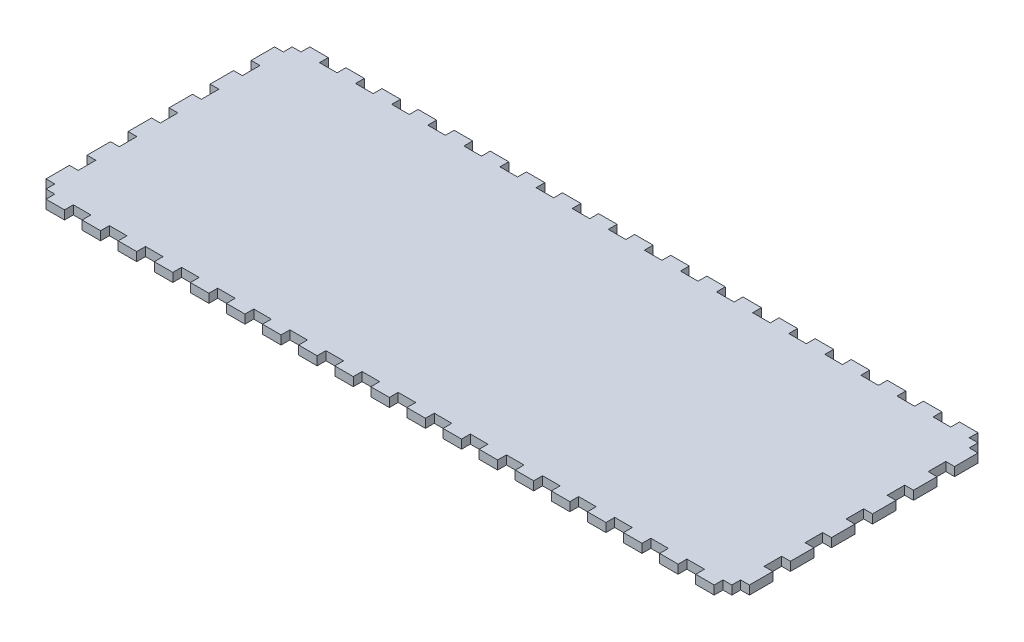
SolidWorks part; units mm, degrees
material "Acrylic (Medium-high impact)"
ref_plane "Front Plane" through (0, 0, 0) normal (0, 0, 1) x (1, 0, 0)
ref_plane "Top Plane" through (0, 0, 0) normal (0, 1, 0) x (1, 0, 0)
ref_plane "Right Plane" through (0, 0, 0) normal (1, 0, 0) x (0, 0, -1)
sketch "Sketch1" plane through (0, 0, 0) normal (0, 1, 0) x (1, 0, 0)
  line L1 (-254, 95.25) -> (254, 95.25)
  line L2 (-254, 95.25) -> (-254, -95.25)
  line L3 (-254, -95.25) -> (254, -95.25)
  line L4 (254, 95.25) -> (254, -95.25)
  point P4 (-254, 0)
  point P6 (0, 95.25)
  dimension "D1" = 190.5
  dimension "D2" = 508
extrude "Boss-Extrude1" add sketch "Sketch1" along normal blind 6.35
sketch "Sketch2" plane through (0, 6.35, 0) normal (0, 1, 0) x (1, 0, 0)
  line L0 (254, -95.25) -> (254, 95.25) construction
  line L1 (-254, 95.25) -> (254, 95.25)
  line L2 (-254, 95.25) -> (-254, -95.25)
  line L3 (-254, -95.25) -> (254, -95.25)
  line L4 (254, 95.25) -> (254, -95.25)
  line L5 (-254, -95.25) -> (254, -95.25) construction
  line L7 (-247.65, 88.9) -> (247.65, 88.9)
  line L8 (-247.65, 88.9) -> (-247.65, -88.9)
  line L9 (-247.65, -88.9) -> (247.65, -88.9)
  line L10 (247.65, 88.9) -> (247.65, -88.9)
  point P7 (-247.65, 0)
  point P14 (-254, 0)
  point P15 (0, -88.9)
  point P16 (0, -95.25)
  point P17 (247.65, 0)
  point P18 (254, 0)
  dimension "D1" = 6.35
  dimension "D2" = 6.35
extrude "Boss-Extrude2" add sketch "Sketch2" along normal blind 298.45
sketch "Sketch3" plane through (0, 0, 95.25) normal (0, 0, 1) x (1, 0, 0)
  line L0 (0, 304.8) -> (0, 0) construction
  line L1 (-254, 304.8) -> (254, 304.8) construction
  line L2 (-247.65, 6.35) -> (247.65, 6.35) construction
  line L4 (-3.302, 283.21) -> (-3.302, 6.35)
  line L5 (-3.302, 6.35) -> (3.302, 6.35)
  line L6 (3.302, 292.354) -> (3.302, 6.35)
  line L7 (3.302, 292.354) -> (-16.256, 292.354)
  line L9 (-5.842, 285.75) -> (-16.256, 285.75)
  line L10 (-16.256, 292.354) -> (-16.256, 285.75)
  line L11 (3.302, 101.6) -> (16.002, 101.6) construction
  line L12 (-254, 0) -> (254, 0) construction
  line L13 (12.827, 88.9) -> (12.827, 101.6) construction
  line L14 (9.652, 88.9) -> (16.002, 88.9)
  line L15 (9.652, 88.9) -> (9.652, 71.9667)
  line L16 (9.652, 71.9667) -> (16.002, 71.9667)
  line L17 (16.002, 88.9) -> (16.002, 71.9667)
  line L18 (9.652, 42.3333) -> (16.002, 42.3333)
  line L19 (9.652, 42.3333) -> (9.652, 59.2667)
  line L20 (9.652, 59.2667) -> (16.002, 59.2667)
  line L21 (16.002, 42.3333) -> (16.002, 59.2667)
  line L26 (9.652, 29.6333) -> (16.002, 29.6333)
  line L27 (9.652, 29.6333) -> (9.652, 12.7)
  line L28 (9.652, 12.7) -> (16.002, 12.7)
  line L29 (16.002, 29.6333) -> (16.002, 12.7)
  line L30 (12.827, 59.2667) -> (12.827, 71.9667) construction
  line L31 (12.827, 29.6333) -> (12.827, 42.3333) construction
  line L32 (12.827, 12.7) -> (12.827, 0) construction
  arc A0 (-3.302, 283.21) -> (-5.842, 285.75) centre (-5.842, 283.21) ccw
  point P5 (0, 6.35)
  dimension "D5" = 2.54
  dimension "D1" = 6.604
  dimension "D2" = 12.954
  dimension "D3" = 6.604
  dimension "D4" = 286.004
  dimension "D6" = 101.6
  dimension "D7" = 12.7
  dimension "D8" = 12.7
  dimension "D9" = 6.35
extrude "Cut-Extrude1" cut sketch "Sketch3" against normal blind 12.7
sketch "Sketch4" plane through (0, 0, -88.9) normal (0, 0, 1) x (1, 0, 0)
  line L0 (-254, 304.8) -> (254, 304.8) construction
  line L1 (-22.606, 304.8) -> (-16.256, 304.8)
  line L2 (-22.606, 304.8) -> (-22.606, 6.35)
  line L3 (-22.606, 6.35) -> (-16.256, 6.35)
  line L4 (-16.256, 304.8) -> (-16.256, 6.35)
  line L5 (6.477, 263.525) -> (6.477, 247.65) construction
  line L6 (-16.256, 292.354) -> (-16.256, 285.75) construction
  line L7 (3.302, 304.8) -> (9.652, 304.8)
  line L8 (3.302, 304.8) -> (3.302, 6.35)
  line L9 (3.302, 6.35) -> (9.652, 6.35)
  line L10 (9.652, 304.8) -> (9.652, 6.35)
  line L11 (247.65, 6.35) -> (-247.65, 6.35) construction
  line L12 (3.302, 6.35) -> (3.302, 292.354) construction
  line L13 (-16.256, 304.8) -> (-22.606, 304.8)
  line L14 (-16.256, 304.8) -> (-16.256, 292.1)
  line L15 (-16.256, 292.1) -> (-22.606, 292.1)
  line L16 (-22.606, 304.8) -> (-22.606, 292.1)
  line L17 (-16.256, 276.225) -> (-22.606, 276.225)
  line L18 (-16.256, 276.225) -> (-16.256, 263.525)
  line L19 (-16.256, 263.525) -> (-22.606, 263.525)
  line L20 (-22.606, 276.225) -> (-22.606, 263.525)
  line L21 (-22.606, 6.35) -> (-16.256, 6.35)
  line L22 (-22.606, 6.35) -> (-22.606, 19.05)
  line L23 (-22.606, 19.05) -> (-16.256, 19.05)
  line L24 (-16.256, 6.35) -> (-16.256, 19.05)
  line L25 (-22.606, 34.925) -> (-16.256, 34.925)
  line L26 (-22.606, 34.925) -> (-22.606, 47.625)
  line L27 (-22.606, 47.625) -> (-16.256, 47.625)
  line L28 (-16.256, 34.925) -> (-16.256, 47.625)
  line L29 (-22.606, 92.075) -> (-16.256, 92.075)
  line L30 (-22.606, 92.075) -> (-22.606, 104.775)
  line L31 (-22.606, 104.775) -> (-16.256, 104.775)
  line L32 (-16.256, 92.075) -> (-16.256, 104.775)
  line L33 (-22.606, 149.225) -> (-16.256, 149.225)
  line L34 (-22.606, 149.225) -> (-22.606, 161.925)
  line L35 (-22.606, 161.925) -> (-16.256, 161.925)
  line L36 (-16.256, 149.225) -> (-16.256, 161.925)
  line L37 (-22.606, 177.8) -> (-16.256, 177.8)
  line L38 (-22.606, 177.8) -> (-22.606, 190.5)
  line L39 (-22.606, 190.5) -> (-16.256, 190.5)
  line L40 (-16.256, 177.8) -> (-16.256, 190.5)
  line L41 (-22.606, 206.375) -> (-16.256, 206.375)
  line L42 (-22.606, 206.375) -> (-22.606, 219.075)
  line L43 (-22.606, 219.075) -> (-16.256, 219.075)
  line L44 (-16.256, 206.375) -> (-16.256, 219.075)
  line L45 (-22.606, 234.95) -> (-16.256, 234.95)
  line L46 (-22.606, 234.95) -> (-22.606, 247.65)
  line L47 (-22.606, 247.65) -> (-16.256, 247.65)
  line L48 (-16.256, 234.95) -> (-16.256, 247.65)
  line L49 (-16.256, 133.35) -> (-22.606, 133.35)
  line L50 (-16.256, 133.35) -> (-16.256, 120.65)
  line L51 (-16.256, 120.65) -> (-22.606, 120.65)
  line L52 (-22.606, 133.35) -> (-22.606, 120.65)
  line L53 (-16.256, 76.2) -> (-22.606, 76.2)
  line L54 (-16.256, 76.2) -> (-16.256, 63.5)
  line L55 (-16.256, 63.5) -> (-22.606, 63.5)
  line L56 (-22.606, 76.2) -> (-22.606, 63.5)
  line L57 (-19.431, 304.8) -> (-19.431, 292.1) construction
  line L58 (-19.431, 292.1) -> (-19.431, 276.225) construction
  line L59 (-19.431, 276.225) -> (-19.431, 263.525) construction
  line L60 (-19.431, 247.65) -> (-19.431, 234.95) construction
  line L61 (-19.431, 234.95) -> (-19.431, 219.075) construction
  line L62 (-19.431, 219.075) -> (-19.431, 206.375) construction
  line L63 (-19.431, 206.375) -> (-19.431, 190.5) construction
  line L64 (-19.431, 190.5) -> (-19.431, 177.8) construction
  line L65 (-19.431, 177.8) -> (-19.431, 161.925) construction
  line L66 (-19.431, 161.925) -> (-19.431, 149.225) construction
  line L67 (-19.431, 133.35) -> (-19.431, 120.65) construction
  line L68 (-19.431, 120.65) -> (-19.431, 104.775) construction
  line L69 (-19.431, 104.775) -> (-19.431, 92.075) construction
  line L70 (-19.431, 92.075) -> (-19.431, 76.2) construction
  line L71 (-19.431, 76.2) -> (-19.431, 63.5) construction
  line L72 (-19.431, 63.5) -> (-19.431, 47.625) construction
  line L73 (-19.431, 47.625) -> (-19.431, 34.925) construction
  line L74 (-19.431, 34.925) -> (-19.431, 19.05) construction
  line L75 (-19.431, 19.05) -> (-19.431, 6.35) construction
  line L76 (-19.431, 149.225) -> (-19.431, 133.35) construction
  line L77 (-19.431, 263.525) -> (-19.431, 247.65) construction
  line L78 (-6.477, 304.8) -> (-6.477, 0) construction
  line L79 (254, 304.8) -> (-254, 304.8) construction
  line L80 (254, 0) -> (-254, 0) construction
  line L81 (-6.477, 8.3493) -> (3.302, 8.3493) construction
  line L82 (-6.477, 8.3493) -> (-16.256, 8.3493) construction
  line L83 (6.477, 149.225) -> (6.477, 133.35) construction
  line L84 (6.477, 19.05) -> (6.477, 6.35) construction
  line L85 (6.477, 34.925) -> (6.477, 19.05) construction
  line L86 (6.477, 47.625) -> (6.477, 34.925) construction
  line L87 (6.477, 63.5) -> (6.477, 47.625) construction
  line L88 (6.477, 76.2) -> (6.477, 63.5) construction
  line L89 (6.477, 92.075) -> (6.477, 76.2) construction
  line L90 (6.477, 104.775) -> (6.477, 92.075) construction
  line L91 (6.477, 120.65) -> (6.477, 104.775) construction
  line L92 (6.477, 133.35) -> (6.477, 120.65) construction
  line L93 (6.477, 161.925) -> (6.477, 149.225) construction
  line L94 (6.477, 177.8) -> (6.477, 161.925) construction
  line L95 (6.477, 190.5) -> (6.477, 177.8) construction
  line L96 (6.477, 206.375) -> (6.477, 190.5) construction
  line L97 (6.477, 219.075) -> (6.477, 206.375) construction
  line L98 (6.477, 234.95) -> (6.477, 219.075) construction
  line L99 (6.477, 247.65) -> (6.477, 234.95) construction
  line L100 (6.477, 276.225) -> (6.477, 263.525) construction
  line L101 (6.477, 292.1) -> (6.477, 276.225) construction
  line L102 (6.477, 304.8) -> (6.477, 292.1) construction
  line L103 (9.652, 76.2) -> (9.652, 63.5)
  line L104 (3.302, 63.5) -> (9.652, 63.5)
  line L105 (3.302, 76.2) -> (3.302, 63.5)
  line L106 (3.302, 76.2) -> (9.652, 76.2)
  line L107 (9.652, 133.35) -> (9.652, 120.65)
  line L108 (3.302, 120.65) -> (9.652, 120.65)
  line L109 (3.302, 133.35) -> (3.302, 120.65)
  line L110 (3.302, 133.35) -> (9.652, 133.35)
  line L111 (3.302, 234.95) -> (3.302, 247.65)
  line L112 (9.652, 247.65) -> (3.302, 247.65)
  line L113 (9.652, 234.95) -> (9.652, 247.65)
  line L114 (9.652, 234.95) -> (3.302, 234.95)
  line L115 (3.302, 206.375) -> (3.302, 219.075)
  line L116 (9.652, 219.075) -> (3.302, 219.075)
  line L117 (9.652, 206.375) -> (9.652, 219.075)
  line L118 (9.652, 206.375) -> (3.302, 206.375)
  line L119 (3.302, 177.8) -> (3.302, 190.5)
  line L120 (9.652, 190.5) -> (3.302, 190.5)
  line L121 (9.652, 177.8) -> (9.652, 190.5)
  line L122 (9.652, 177.8) -> (3.302, 177.8)
  line L123 (3.302, 149.225) -> (3.302, 161.925)
  line L124 (9.652, 161.925) -> (3.302, 161.925)
  line L125 (9.652, 149.225) -> (9.652, 161.925)
  line L126 (9.652, 149.225) -> (3.302, 149.225)
  line L127 (3.302, 92.075) -> (3.302, 104.775)
  line L128 (9.652, 104.775) -> (3.302, 104.775)
  line L129 (9.652, 92.075) -> (9.652, 104.775)
  line L130 (9.652, 92.075) -> (3.302, 92.075)
  line L131 (3.302, 34.925) -> (3.302, 47.625)
  line L132 (9.652, 47.625) -> (3.302, 47.625)
  line L133 (9.652, 34.925) -> (9.652, 47.625)
  line L134 (9.652, 34.925) -> (3.302, 34.925)
  line L135 (3.302, 6.35) -> (3.302, 19.05)
  line L136 (9.652, 19.05) -> (3.302, 19.05)
  line L137 (9.652, 6.35) -> (9.652, 19.05)
  line L138 (9.652, 6.35) -> (3.302, 6.35)
  line L139 (9.652, 276.225) -> (9.652, 263.525)
  line L140 (3.302, 263.525) -> (9.652, 263.525)
  line L141 (3.302, 276.225) -> (3.302, 263.525)
  line L142 (3.302, 276.225) -> (9.652, 276.225)
  line L143 (9.652, 304.8) -> (9.652, 292.1)
  line L144 (3.302, 292.1) -> (9.652, 292.1)
  line L145 (3.302, 304.8) -> (3.302, 292.1)
  line L146 (3.302, 304.8) -> (9.652, 304.8)
  line L147 (3.302, 304.8) -> (3.302, 6.35)
  line L148 (9.652, 6.35) -> (3.302, 6.35)
  line L149 (9.652, 304.8) -> (9.652, 6.35)
  line L150 (9.652, 304.8) -> (3.302, 304.8)
  point P14 (-16.256, 289.052)
  dimension "D1" = 6.35
  dimension "D2" = 12.7
extrude "Cut-Extrude2" cut sketch "Sketch4" against normal up to next (6.35 mm away) contours L17 L4 L15 L2 | L2 L47 L4 L19 | L45 L2 L43 L4 | L41 L2 L39 L4 | L37 L2 L35 L4 | L49 L4 L33 L2 | L4 L51 L2 L31 | L53 L4 L29 L2 | L4 L55 L2 L27 | L25 L2 L23 L4
ref_plane "Plane1" through (-6.477, 0, 0) normal (-1, 0, 0) x (0, 0, 1)
mirror "Mirror1" about plane through (-6.477, 0, 0) normal (-1, 0, 0) of "Cut-Extrude2"
sketch "Sketch5" plane through (0, 0, 0) normal (0, -1, 0) x (-1, 0, 0)
  line L0 (-227.9316, -95.25) -> (-227.9316, -88.9)
  line L1 (-247.65, 88.9) -> (247.65, 88.9)
  line L2 (-247.65, 88.9) -> (-247.65, -88.9)
  line L3 (-247.65, -88.9) -> (247.65, -88.9)
  line L4 (247.65, 88.9) -> (247.65, -88.9)
  line L5 (-254, -95.25) -> (-241.3, -95.25)
  line L6 (-254, -95.25) -> (-254, -88.9)
  line L7 (-254, -88.9) -> (-241.3, -88.9)
  line L8 (-241.3, -95.25) -> (-241.3, -88.9)
  line L9 (-227.9316, -95.25) -> (-215.2316, -95.25)
  line L10 (-227.9316, -88.9) -> (-215.2316, -88.9)
  line L11 (-215.2316, -95.25) -> (-215.2316, -88.9)
  line L12 (-201.8632, -95.25) -> (-201.8632, -88.9)
  line L13 (-201.8632, -95.25) -> (-189.1632, -95.25)
  line L14 (-201.8632, -88.9) -> (-189.1632, -88.9)
  line L15 (-189.1632, -95.25) -> (-189.1632, -88.9)
  line L16 (-175.7947, -95.25) -> (-175.7947, -88.9)
  line L17 (-175.7947, -95.25) -> (-163.0947, -95.25)
  line L18 (-175.7947, -88.9) -> (-163.0947, -88.9)
  line L19 (-163.0947, -95.25) -> (-163.0947, -88.9)
  line L20 (-149.7263, -95.25) -> (-149.7263, -88.9)
  line L21 (-149.7263, -95.25) -> (-137.0263, -95.25)
  line L22 (-149.7263, -88.9) -> (-137.0263, -88.9)
  line L23 (-137.0263, -95.25) -> (-137.0263, -88.9)
  line L24 (-123.6579, -95.25) -> (-123.6579, -88.9)
  line L25 (-123.6579, -95.25) -> (-110.9579, -95.25)
  line L26 (-123.6579, -88.9) -> (-110.9579, -88.9)
  line L27 (-110.9579, -95.25) -> (-110.9579, -88.9)
  line L28 (-97.5895, -95.25) -> (-97.5895, -88.9)
  line L29 (-97.5895, -95.25) -> (-84.8895, -95.25)
  line L30 (-97.5895, -88.9) -> (-84.8895, -88.9)
  line L31 (-84.8895, -95.25) -> (-84.8895, -88.9)
  line L32 (-71.5211, -95.25) -> (-71.5211, -88.9)
  line L33 (-71.5211, -95.25) -> (-58.8211, -95.25)
  line L34 (-71.5211, -88.9) -> (-58.8211, -88.9)
  line L35 (-58.8211, -95.25) -> (-58.8211, -88.9)
  line L36 (-45.4526, -95.25) -> (-45.4526, -88.9)
  line L37 (-45.4526, -95.25) -> (-32.7526, -95.25)
  line L38 (-45.4526, -88.9) -> (-32.7526, -88.9)
  line L39 (-32.7526, -95.25) -> (-32.7526, -88.9)
  line L40 (-19.3842, -95.25) -> (-19.3842, -88.9)
  line L41 (-19.3842, -95.25) -> (-6.6842, -95.25)
  line L42 (-19.3842, -88.9) -> (-6.6842, -88.9)
  line L43 (-6.6842, -95.25) -> (-6.6842, -88.9)
  line L44 (6.6842, -95.25) -> (6.6842, -88.9)
  line L45 (6.6842, -95.25) -> (19.3842, -95.25)
  line L46 (6.6842, -88.9) -> (19.3842, -88.9)
  line L47 (19.3842, -95.25) -> (19.3842, -88.9)
  line L48 (32.7526, -95.25) -> (32.7526, -88.9)
  line L49 (32.7526, -95.25) -> (45.4526, -95.25)
  line L50 (32.7526, -88.9) -> (45.4526, -88.9)
  line L51 (45.4526, -95.25) -> (45.4526, -88.9)
  line L52 (58.8211, -95.25) -> (58.8211, -88.9)
  line L53 (58.8211, -95.25) -> (71.5211, -95.25)
  line L54 (58.8211, -88.9) -> (71.5211, -88.9)
  line L55 (71.5211, -95.25) -> (71.5211, -88.9)
  line L56 (84.8895, -95.25) -> (84.8895, -88.9)
  line L57 (84.8895, -95.25) -> (97.5895, -95.25)
  line L58 (84.8895, -88.9) -> (97.5895, -88.9)
  line L59 (97.5895, -95.25) -> (97.5895, -88.9)
  line L60 (110.9579, -95.25) -> (110.9579, -88.9)
  line L61 (110.9579, -95.25) -> (123.6579, -95.25)
  line L62 (110.9579, -88.9) -> (123.6579, -88.9)
  line L63 (123.6579, -95.25) -> (123.6579, -88.9)
  line L64 (137.0263, -95.25) -> (137.0263, -88.9)
  line L65 (137.0263, -95.25) -> (149.7263, -95.25)
  line L66 (137.0263, -88.9) -> (149.7263, -88.9)
  line L67 (149.7263, -95.25) -> (149.7263, -88.9)
  line L68 (163.0947, -95.25) -> (163.0947, -88.9)
  line L69 (163.0947, -95.25) -> (175.7947, -95.25)
  line L70 (163.0947, -88.9) -> (175.7947, -88.9)
  line L71 (175.7947, -95.25) -> (175.7947, -88.9)
  line L72 (189.1632, -95.25) -> (189.1632, -88.9)
  line L73 (189.1632, -95.25) -> (201.8632, -95.25)
  line L74 (189.1632, -88.9) -> (201.8632, -88.9)
  line L75 (201.8632, -95.25) -> (201.8632, -88.9)
  line L76 (215.2316, -95.25) -> (215.2316, -88.9)
  line L77 (215.2316, -95.25) -> (227.9316, -95.25)
  line L78 (215.2316, -88.9) -> (227.9316, -88.9)
  line L79 (227.9316, -95.25) -> (227.9316, -88.9)
  line L80 (241.3, -95.25) -> (241.3, -88.9)
  line L81 (241.3, -95.25) -> (254, -95.25)
  line L82 (241.3, -88.9) -> (254, -88.9)
  line L83 (254, -95.25) -> (254, -88.9)
  line L84 (-167.64, 0) -> (167.64, 0) construction
  line L85 (254, 95.25) -> (254, 88.9)
  line L86 (241.3, 88.9) -> (254, 88.9)
  line L87 (241.3, 95.25) -> (254, 95.25)
  line L88 (241.3, 95.25) -> (241.3, 88.9)
  line L89 (227.9316, 95.25) -> (227.9316, 88.9)
  line L90 (215.2316, 88.9) -> (227.9316, 88.9)
  line L91 (215.2316, 95.25) -> (227.9316, 95.25)
  line L92 (215.2316, 95.25) -> (215.2316, 88.9)
  line L93 (201.8632, 95.25) -> (201.8632, 88.9)
  line L94 (189.1632, 88.9) -> (201.8632, 88.9)
  line L95 (189.1632, 95.25) -> (201.8632, 95.25)
  line L96 (189.1632, 95.25) -> (189.1632, 88.9)
  line L97 (175.7947, 95.25) -> (175.7947, 88.9)
  line L98 (163.0947, 88.9) -> (175.7947, 88.9)
  line L99 (163.0947, 95.25) -> (175.7947, 95.25)
  line L100 (163.0947, 95.25) -> (163.0947, 88.9)
  line L101 (149.7263, 95.25) -> (149.7263, 88.9)
  line L102 (137.0263, 88.9) -> (149.7263, 88.9)
  line L103 (137.0263, 95.25) -> (149.7263, 95.25)
  line L104 (137.0263, 95.25) -> (137.0263, 88.9)
  line L105 (123.6579, 95.25) -> (123.6579, 88.9)
  line L106 (110.9579, 88.9) -> (123.6579, 88.9)
  line L107 (110.9579, 95.25) -> (123.6579, 95.25)
  line L108 (110.9579, 95.25) -> (110.9579, 88.9)
  line L109 (97.5895, 95.25) -> (97.5895, 88.9)
  line L110 (84.8895, 88.9) -> (97.5895, 88.9)
  line L111 (84.8895, 95.25) -> (97.5895, 95.25)
  line L112 (84.8895, 95.25) -> (84.8895, 88.9)
  line L113 (71.5211, 95.25) -> (71.5211, 88.9)
  line L114 (58.8211, 88.9) -> (71.5211, 88.9)
  line L115 (58.8211, 95.25) -> (71.5211, 95.25)
  line L116 (58.8211, 95.25) -> (58.8211, 88.9)
  line L117 (45.4526, 95.25) -> (45.4526, 88.9)
  line L118 (32.7526, 88.9) -> (45.4526, 88.9)
  line L119 (32.7526, 95.25) -> (45.4526, 95.25)
  line L120 (32.7526, 95.25) -> (32.7526, 88.9)
  line L121 (19.3842, 95.25) -> (19.3842, 88.9)
  line L122 (6.6842, 88.9) -> (19.3842, 88.9)
  line L123 (6.6842, 95.25) -> (19.3842, 95.25)
  line L124 (6.6842, 95.25) -> (6.6842, 88.9)
  line L125 (-6.6842, 95.25) -> (-6.6842, 88.9)
  line L126 (-19.3842, 88.9) -> (-6.6842, 88.9)
  line L127 (-19.3842, 95.25) -> (-6.6842, 95.25)
  line L128 (-19.3842, 95.25) -> (-19.3842, 88.9)
  line L129 (-32.7526, 95.25) -> (-32.7526, 88.9)
  line L130 (-45.4526, 88.9) -> (-32.7526, 88.9)
  line L131 (-45.4526, 95.25) -> (-32.7526, 95.25)
  line L132 (-45.4526, 95.25) -> (-45.4526, 88.9)
  line L133 (-58.8211, 95.25) -> (-58.8211, 88.9)
  line L134 (-71.5211, 88.9) -> (-58.8211, 88.9)
  line L135 (-71.5211, 95.25) -> (-58.8211, 95.25)
  line L136 (-71.5211, 95.25) -> (-71.5211, 88.9)
  line L137 (-84.8895, 95.25) -> (-84.8895, 88.9)
  line L138 (-97.5895, 88.9) -> (-84.8895, 88.9)
  line L139 (-97.5895, 95.25) -> (-84.8895, 95.25)
  line L140 (-97.5895, 95.25) -> (-97.5895, 88.9)
  line L141 (-110.9579, 95.25) -> (-110.9579, 88.9)
  line L142 (-123.6579, 88.9) -> (-110.9579, 88.9)
  line L143 (-123.6579, 95.25) -> (-110.9579, 95.25)
  line L144 (-123.6579, 95.25) -> (-123.6579, 88.9)
  line L145 (-137.0263, 95.25) -> (-137.0263, 88.9)
  line L146 (-149.7263, 88.9) -> (-137.0263, 88.9)
  line L147 (-149.7263, 95.25) -> (-137.0263, 95.25)
  line L148 (-149.7263, 95.25) -> (-149.7263, 88.9)
  line L149 (-163.0947, 95.25) -> (-163.0947, 88.9)
  line L150 (-175.7947, 88.9) -> (-163.0947, 88.9)
  line L151 (-175.7947, 95.25) -> (-163.0947, 95.25)
  line L152 (-175.7947, 95.25) -> (-175.7947, 88.9)
  line L153 (-189.1632, 95.25) -> (-189.1632, 88.9)
  line L154 (-201.8632, 88.9) -> (-189.1632, 88.9)
  line L155 (-201.8632, 95.25) -> (-189.1632, 95.25)
  line L156 (-201.8632, 95.25) -> (-201.8632, 88.9)
  line L157 (-215.2316, 95.25) -> (-215.2316, 88.9)
  line L158 (-227.9316, 88.9) -> (-215.2316, 88.9)
  line L159 (-227.9316, 95.25) -> (-215.2316, 95.25)
  line L160 (-241.3, 95.25) -> (-241.3, 88.9)
  line L161 (-254, 88.9) -> (-241.3, 88.9)
  line L162 (-254, 95.25) -> (-254, 88.9)
  line L163 (-254, 95.25) -> (-241.3, 95.25)
  line L164 (-247.65, 88.9) -> (247.65, 88.9)
  line L165 (-227.9316, 95.25) -> (-227.9316, 88.9)
  line L166 (-254, 65.6167) -> (-254, 52.9167)
  line L167 (-254, 95.25) -> (-247.65, 95.25)
  line L168 (-254, 95.25) -> (-254, 82.55)
  line L169 (-254, 82.55) -> (-247.65, 82.55)
  line L170 (-247.65, 95.25) -> (-247.65, 82.55)
  line L171 (-254, 65.6167) -> (-247.65, 65.6167)
  line L172 (-247.65, 65.6167) -> (-247.65, 52.9167)
  line L173 (-254, 52.9167) -> (-247.65, 52.9167)
  line L174 (-254, 35.9833) -> (-254, 23.2833)
  line L175 (-254, 35.9833) -> (-247.65, 35.9833)
  line L176 (-247.65, 35.9833) -> (-247.65, 23.2833)
  line L177 (-254, 23.2833) -> (-247.65, 23.2833)
  line L178 (-254, 6.35) -> (-254, -6.35)
  line L179 (-254, 6.35) -> (-247.65, 6.35)
  line L180 (-247.65, 6.35) -> (-247.65, -6.35)
  line L181 (-254, -6.35) -> (-247.65, -6.35)
  line L182 (-254, -23.2833) -> (-254, -35.9833)
  line L183 (-254, -23.2833) -> (-247.65, -23.2833)
  line L184 (-247.65, -23.2833) -> (-247.65, -35.9833)
  line L185 (-254, -35.9833) -> (-247.65, -35.9833)
  line L186 (-254, -52.9167) -> (-254, -65.6167)
  line L187 (-254, -52.9167) -> (-247.65, -52.9167)
  line L188 (-247.65, -52.9167) -> (-247.65, -65.6167)
  line L189 (-254, -65.6167) -> (-247.65, -65.6167)
  line L190 (-254, -82.55) -> (-254, -95.25)
  line L191 (-254, -82.55) -> (-247.65, -82.55)
  line L192 (-247.65, -82.55) -> (-247.65, -95.25)
  line L193 (-254, -95.25) -> (-247.65, -95.25)
  line L194 (0, 140.1848) -> (0, -140.1848) construction
  line L195 (254, -95.25) -> (247.65, -95.25)
  line L196 (247.65, -82.55) -> (247.65, -95.25)
  line L197 (254, -82.55) -> (247.65, -82.55)
  line L198 (254, -82.55) -> (254, -95.25)
  line L199 (254, -65.6167) -> (247.65, -65.6167)
  line L200 (247.65, -52.9167) -> (247.65, -65.6167)
  line L201 (254, -52.9167) -> (247.65, -52.9167)
  line L202 (254, -52.9167) -> (254, -65.6167)
  line L203 (254, -35.9833) -> (247.65, -35.9833)
  line L204 (247.65, -23.2833) -> (247.65, -35.9833)
  line L205 (254, -23.2833) -> (247.65, -23.2833)
  line L206 (254, -23.2833) -> (254, -35.9833)
  line L207 (254, -6.35) -> (247.65, -6.35)
  line L208 (247.65, 6.35) -> (247.65, -6.35)
  line L209 (254, 6.35) -> (247.65, 6.35)
  line L210 (254, 6.35) -> (254, -6.35)
  line L211 (254, 23.2833) -> (247.65, 23.2833)
  line L212 (247.65, 35.9833) -> (247.65, 23.2833)
  line L213 (254, 35.9833) -> (247.65, 35.9833)
  line L214 (254, 35.9833) -> (254, 23.2833)
  line L215 (254, 52.9167) -> (247.65, 52.9167)
  line L216 (247.65, 65.6167) -> (247.65, 52.9167)
  line L217 (254, 65.6167) -> (247.65, 65.6167)
  line L218 (247.65, 95.25) -> (247.65, 82.55)
  line L219 (254, 82.55) -> (247.65, 82.55)
  line L220 (254, 95.25) -> (254, 82.55)
  line L221 (254, 95.25) -> (247.65, 95.25)
  line L222 (254, 65.6167) -> (254, 52.9167)
  line L223 (254, 95.25) -> (254, 88.9)
  line L224 (254, -95.25) -> (254, -88.9)
  line L225 (247.65, 88.9) -> (247.65, -88.9)
  line M114 (254, -95.25) -> (254, 95.25)
  line M115 (254, 95.25) -> (-254, 95.25)
  line M116 (-254, 95.25) -> (-254, -95.25)
  line M117 (-254, -95.25) -> (254, -95.25)
  dimension "D1" = 12.7
  dimension "D3" = 6.35
  dimension "D5" = 12.7
  dimension "D2" = 20
  dimension "D4" = 7
sketch "Sketch6" plane through (0, 0, 95.25) normal (0, 0, 1) x (1, 0, 0)
  line L0 (-247.65, 6.35) -> (-3.302, 6.35) construction
  line L1 (-305.4825, 341.0254) -> (326.3346, 341.0254)
  line L2 (-305.4825, 341.0254) -> (-305.4825, 6.35)
  line L3 (-305.4825, 6.35) -> (326.3346, 6.35)
  line L4 (326.3346, 341.0254) -> (326.3346, 6.35)
extrude "Cut-Extrude3" cut sketch "Sketch6" against normal through all
extrude "Cut-Extrude4" cut sketch "Sketch5" against normal through all contours L196 L3 L80 M117 | L82 L196 L81 M114 | L197 L4 L82 M114 | L201 L4 L199 M114 | L205 L4 L203 M114 | L209 L4 L207 M114 | L213 L4 L211 M114 | L217 L4 L215 M114 | L219 L86 L4 M114 | L218 L86 M115 M114 | L218 L87 L88 L1 | L92 L1 L89 M115 | L96 L1 L93 M115 | L100 L1 L97 M115 | L104 L1 L101 M115 | L108 L1 L105 M115 | L112 L1 L109 M115 | L116 L1 L113 M115 | L120 L1 L117 M115 | L124 L1 L121 M115 | L128 L1 L125 M115 | L132 L1 L129 M115 | L136 L1 L133 M115 | L140 L1 L137 M115 | L144 L1 L141 M115 | L148 L1 L145 M115 | L152 L1 L149 M115 | L156 L1 L153 M115 | L75 L3 L72 M117 | L71 L3 L68 M117 | L67 L3 L64 M117 | L59 L3 L56 M117 | L55 L3 L52 M117 | L79 L3 L76 M117 | L63 L3 L60 M117 | L51 L3 L48 M117 | L47 L3 L44 M117 | L35 L3 L32 M117 | L31 L3 L28 M117 | L27 L3 L24 M117 | L23 L3 L20 M117 | L15 L3 L12 M117 | L11 L3 L0 M117 | L3 L192 L5 L8 | L192 L7 M116 M117 | L191 L7 L2 M116 | L189 L2 L187 M116 | L185 L2 L183 M116 | L181 L2 L179 M116 | L177 L2 L175 M116 | L173 L2 L171 M116 | L169 L2 L161 M116 | L170 L163 L161 M116 | L170 L1 L160 M115 | L165 L1 L157 M115 | L43 L3 L40 M117 | L39 L3 L36 M117 | L19 L3 L16 M117
